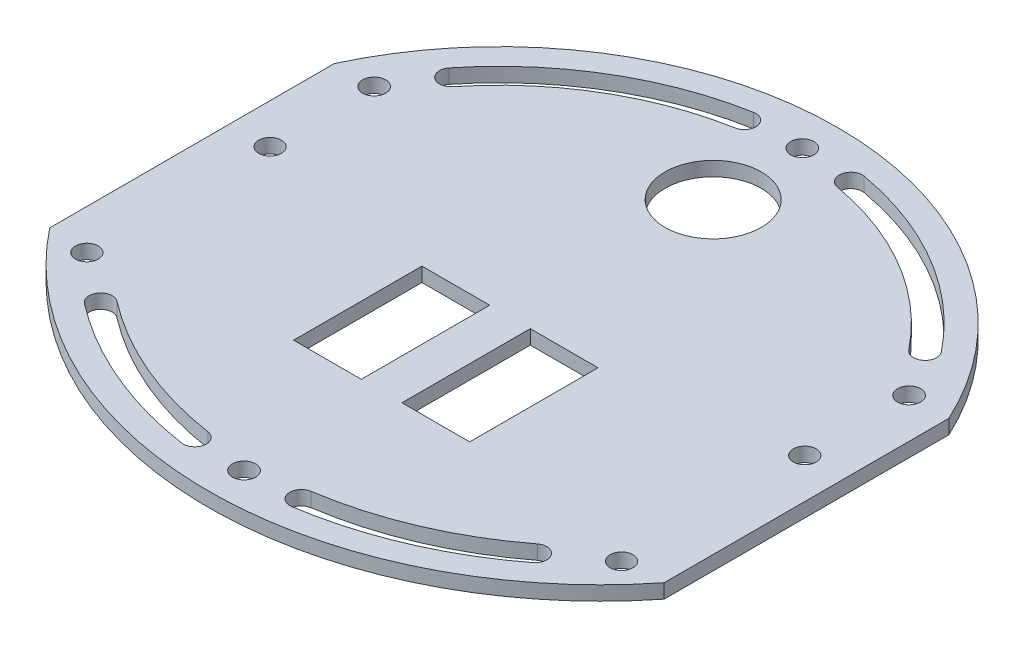
SolidWorks part; units mm, degrees
material "Acrylic (Medium-high impact)"
ref_plane "Front Plane" through (0, 0, 0) normal (0, 0, 1) x (1, 0, 0)
ref_plane "Top Plane" through (0, 0, 0) normal (0, 1, 0) x (1, 0, 0)
ref_plane "Right Plane" through (0, 0, 0) normal (1, 0, 0) x (0, 0, -1)
sketch "Sketch1" plane through (0, 0, 0) normal (0, 1, 0) x (1, 0, 0)
  line L0 (86.2, 39.9319) -> (86.2, -39.9319)
  line L5 (0, -1000) -> (0, 49000) construction
  line L6 (-86.2, 39.9319) -> (-86.2, -39.9319)
  arc A4 (-86.2, -39.9319) -> (86.2, -39.9319) centre (0, 0) ccw construction
  arc A5 (86.2, 39.9319) -> (-86.2, 39.9319) centre (0, 0) ccw
  arc A7 (-86.2, -39.9319) -> (86.2, -39.9319) centre (0, 28.4022) ccw
  dimension "D1" = 172.4
  dimension "D2" = 95
  dimension "D3" = 110
extrude "Boss-Extrude1" add sketch "Sketch1" along normal mid plane 4
sketch "Sketch2" plane through (0, 0, 0) normal (0, 1, 0) x (1, 0, 0)
  line L0 (0, -1000) -> (0, 49000) construction
  line L1 (-86.2, 39.9319) -> (-86.2, -39.9319) construction
  line L2 (-75, 10.7) -> (-75, -40.7) construction
  circle A0 centre (-75, 10.7) radius 3.2
  circle A1 centre (-75, -40.7) radius 3.2
  circle A2 centre (75, -40.7) radius 3.2
  circle A3 centre (75, 10.7) radius 3.2
  circle A4 centre (0, 0) radius 95 construction
  arc A5 (86.2, 39.9319) -> (-86.2, 39.9319) centre (0, 0) ccw construction
  circle A6 centre (0, -71.5978) radius 3.25
  arc A7 (-75.8168, -31.7008) -> (75.8168, -31.7008) centre (0, 28.4022) ccw construction
  circle A8 centre (0, 85) radius 3.25
  arc A9 (-80.9105, -35.7387) -> (-73.8995, -43.7048) centre (0, 28.4022) ccw construction
  arc A10 (14.4716, -67.2593) -> (15.4439, -73.6862) centre (14.9578, -70.4728) ccw
  arc A11 (-78.3636, -33.7197) -> (78.3636, -33.7197) centre (0, 28.4022) ccw
  arc A12 (-78.3636, -33.7197) -> (78.3636, -33.7197) centre (0, 28.4022) ccw construction
  arc A13 (62.9367, -53.4484) -> (58.9746, -48.2956) centre (60.9557, -50.872) ccw
  arc A14 (-75.0363, 39.9319) -> (75.0363, 39.9319) centre (0, 0) cw construction
  arc A15 (-75.8168, -31.7008) -> (-75, -32.717) centre (0, 28.4022) ccw construction
  arc A16 (-80.9105, -35.7387) -> (80.9105, -35.7387) centre (0, 28.4022) ccw construction
  arc A17 (14.4716, -67.2593) -> (58.9746, -48.2956) centre (0, 28.4022) ccw
  arc A18 (15.4439, -73.6862) -> (62.9367, -53.4484) centre (0, 28.4022) ccw
  arc A19 (-62.9367, -53.4484) -> (-58.9746, -48.2956) centre (-60.9557, -50.872) cw
  arc A20 (-15.4439, -73.6862) -> (-62.9367, -53.4484) centre (0, 28.4022) cw
  arc A21 (-14.4716, -67.2593) -> (-15.4439, -73.6862) centre (-14.9578, -70.4728) cw
  arc A22 (-14.4716, -67.2593) -> (-58.9746, -48.2956) centre (0, 28.4022) cw
  arc A23 (-63.9416, 50.9365) -> (-69.0257, 54.9865) centre (-66.4836, 52.9615) cw
  arc A24 (-15.5128, 86.8759) -> (-69.0257, 54.9865) centre (0, 0) ccw
  arc A25 (15.5128, 86.8759) -> (14.3702, 80.4771) centre (14.9415, 83.6765) ccw
  arc A26 (63.9416, 50.9365) -> (69.0257, 54.9865) centre (66.4836, 52.9615) ccw
  arc A27 (14.3702, 80.4771) -> (63.9416, 50.9365) centre (0, 0) cw
  arc A28 (-15.5128, 86.8759) -> (-14.3702, 80.4771) centre (-14.9415, 83.6765) cw
  arc A29 (15.5128, 86.8759) -> (69.0257, 54.9865) centre (0, 0) cw
  arc A30 (-14.3702, 80.4771) -> (-63.9416, 50.9365) centre (0, 0) ccw
  circle A31 centre (-75.0363, 39.9319) radius 3.25
  circle A32 centre (75.0363, 39.9319) radius 3.25
  point P9 (-75, -15)
  dimension "D1" = 6.4
  dimension "D5" = 6.5
  dimension "D6" = 10
  dimension "D7" = 50
  dimension "D11" = 10
  dimension "D12" = 6.5
  dimension "D2" = 51.4
  dimension "D3" = 11.2
  dimension "D4" = 15
  dimension "D8" = 15
  dimension "D14" = 60
  dimension "D15" = 15
  dimension "D9" = 3.25
  dimension "D10" = 3.25
extrude "Cut-Holes" cut sketch "Sketch2" against normal through all both and the other way through all
sketch "Sketch3" plane through (0, 0, 0) normal (0, 1, 0) x (1, 0, 0)
  line L0 (-75, 10.7) -> (-75, -40.7) construction
  line L5 (75, -40.7) -> (75, 10.7) construction
  line L6 (75, -15) -> (-75, -15) construction
  line L7 (0, -1000) -> (0, 49000) construction
  line L8 (-24.7, 3) -> (-5.7, 3)
  line L9 (-24.7, 3) -> (-24.7, -33)
  line L10 (-24.7, -33) -> (-5.7, -33)
  line L11 (-5.7, 3) -> (-5.7, -33)
  line L12 (-24.7, 3) -> (-5.7, -33) construction
  line L13 (-24.7, -33) -> (-5.7, 3) construction
  line L14 (5.7, 3) -> (5.7, -33)
  line L15 (24.7, -33) -> (5.7, -33)
  line L16 (24.7, 3) -> (24.7, -33)
  line L17 (24.7, 3) -> (5.7, 3)
  line L18 (-86.2, 39.9319) -> (-86.2, -39.9319) construction
  circle A0 centre (0, 60) radius 11.5 construction
  circle A1 centre (0, 60) radius 13.5
  point P15 (-15.2, -15)
  point P39 (0, 0)
  dimension "D1" = 23
  dimension "D2" = 60
  dimension "D4" = 19
  dimension "D5" = 36
  dimension "D6" = 61.5
  dimension "D3" = 2
extrude "Cut-Extrude2" cut sketch "Sketch3" against normal through all both and the other way through all
